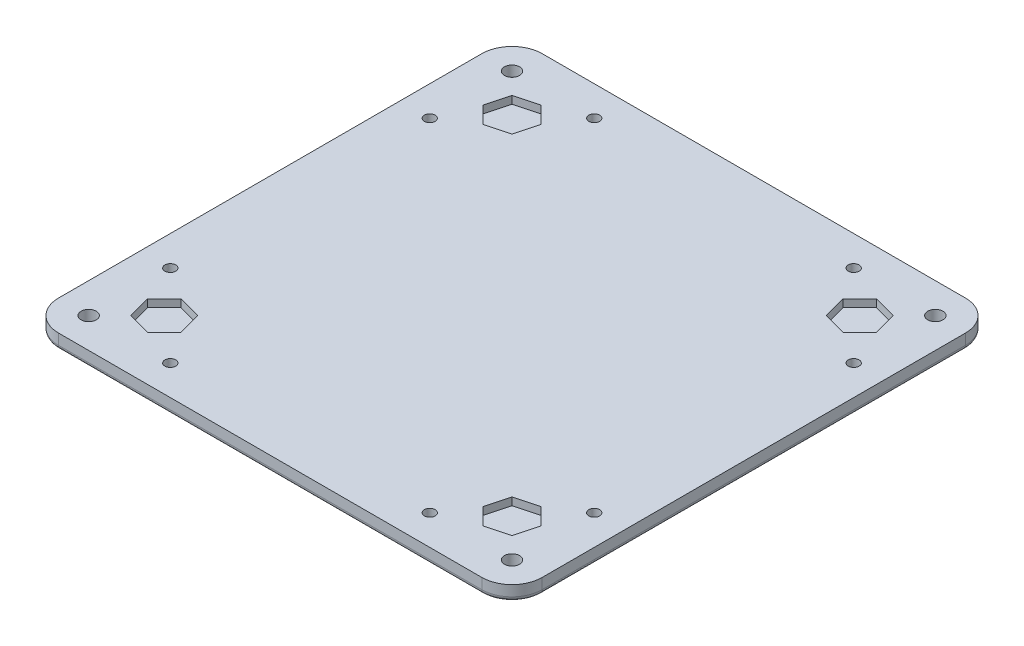
SolidWorks part; units mm, degrees
ref_plane "Front Plane" through (0, 0, 0) normal (0, 0, 1) x (1, 0, 0)
ref_plane "Top Plane" through (0, 0, 0) normal (0, 1, 0) x (1, 0, 0)
ref_plane "Right Plane" through (0, 0, 0) normal (1, 0, 0) x (0, 0, -1)
sketch "Sketch1" plane through (0, 0, 0) normal (0, 1, 0) x (1, 0, 0)
  line L1 (0, 0) -> (203.2, 0)
  line L2 (0, 0) -> (0, 203.2)
  line L3 (0, 203.2) -> (203.2, 203.2)
  line L4 (203.2, 0) -> (203.2, 203.2)
  dimension "D1" = 203.2
  dimension "D2" = 203.2
extrude "Boss-Extrude1" add sketch "Sketch1" along normal blind 6.35
fillet "Fillet1" radius 12.7 4 edges at (0, 3.175, -203.2) (0, 3.175, 0) (203.2, 3.175, 0) (203.2, 3.175, -203.2)
sketch "Sketch2" plane through (0, 0, 0) normal (0, -1, 0) x (1, 0, 0)
  circle A0 centre (12.7, -12.7) radius 3.175
  circle A1 centre (190.5, -12.7) radius 3.175
  circle A2 centre (190.5, -190.5) radius 3.175
  circle A3 centre (12.7, -190.5) radius 3.175
  arc A4 (190.5, -203.2) -> (203.2, -190.5) centre (190.5, -190.5) ccw construction
  arc A5 (12.7, 0) -> (0, -12.7) centre (12.7, -12.7) ccw construction
  dimension "D1" = 6.35
extrude "Cut-Extrude1" cut sketch "Sketch2" against normal through all
sketch "Sketch22" plane through (0, 6.35, 0) normal (0, 1, 0) x (1, 0, 0)
  line L17 (190.5, 203.2) -> (12.7, 203.2) construction
  line L18 (203.2, 12.7) -> (203.2, 190.5) construction
  line L21 (181.6542, 181.6542) -> (172.0521, 184.2271)
  line L22 (172.0521, 184.2271) -> (165.0229, 177.1979)
  line L23 (165.0229, 177.1979) -> (167.5958, 167.5958)
  line L24 (167.5958, 167.5958) -> (177.1979, 165.0229)
  line L25 (177.1979, 165.0229) -> (184.2271, 172.0521)
  line L26 (184.2271, 172.0521) -> (181.6542, 181.6542)
  line L27 (174.625, 174.625) -> (190.5, 190.5) construction
  line L28 (101.6, 203.2) -> (101.6, 0) construction
  line L29 (12.7, 0) -> (190.5, 0) construction
  line L30 (203.2, 101.6) -> (0, 101.6) construction
  line L31 (0, 190.5) -> (0, 12.7) construction
  line L32 (28.575, 174.625) -> (12.7, 190.5) construction
  line L33 (18.9729, 172.0521) -> (21.5458, 181.6542)
  line L34 (26.0021, 165.0229) -> (18.9729, 172.0521)
  line L35 (35.6042, 167.5958) -> (26.0021, 165.0229)
  line L36 (38.1771, 177.1979) -> (35.6042, 167.5958)
  line L37 (31.1479, 184.2271) -> (38.1771, 177.1979)
  line L38 (21.5458, 181.6542) -> (31.1479, 184.2271)
  line L39 (174.625, 28.575) -> (190.5, 12.7) construction
  line L40 (184.2271, 31.1479) -> (181.6542, 21.5458)
  line L41 (177.1979, 38.1771) -> (184.2271, 31.1479)
  line L42 (167.5958, 35.6042) -> (177.1979, 38.1771)
  line L43 (165.0229, 26.0021) -> (167.5958, 35.6042)
  line L44 (172.0521, 18.9729) -> (165.0229, 26.0021)
  line L45 (181.6542, 21.5458) -> (172.0521, 18.9729)
  line L46 (28.575, 28.575) -> (12.7, 12.7) construction
  line L47 (21.5458, 21.5458) -> (31.1479, 18.9729)
  line L48 (31.1479, 18.9729) -> (38.1771, 26.0021)
  line L49 (38.1771, 26.0021) -> (35.6042, 35.6042)
  line L50 (35.6042, 35.6042) -> (26.0021, 38.1771)
  line L51 (26.0021, 38.1771) -> (18.9729, 31.1479)
  line L52 (18.9729, 31.1479) -> (21.5458, 21.5458)
  circle A0 centre (174.625, 174.625) radius 8.609 construction
  circle A1 centre (28.575, 174.625) radius 8.609 construction
  circle A2 centre (174.625, 28.575) radius 8.609 construction
  circle A3 centre (28.575, 28.575) radius 8.609 construction
  dimension "D5" = 17.218
  dimension "D3" = 28.575
  dimension "D4" = 28.575
extrude "Cut-Extrude2" cut sketch "Sketch22" against normal blind 3.175
fillet "Fillet2" radius 1.905 12 edges at (3.7197, 0, -3.7197) (101.6, 0, 0) (199.4803, 0, -3.7197) (203.2, 0, -101.6) (199.4803, 0, -199.4803) (101.6, 0, -203.2) (3.7197, 0, -199.4803) (0, 0, -101.6) (12.7, 0, -15.875) (190.5, 0, -15.875) (190.5, 0, -193.675) (12.7, 0, -193.675)
sketch "Sketch28" plane through (0, 6.35, 0) normal (0, 1, 0) x (1, 0, 0)
  line L0 (190.5, 203.2) -> (12.7, 203.2) construction
  line L1 (203.2, 12.7) -> (203.2, 190.5) construction
  line L2 (12.7, 0) -> (190.5, 0) construction
  line L4 (0, 190.5) -> (0, 12.7) construction
  circle A0 centre (47.117, 190.627) radius 2.286
  circle A1 centre (156.083, 190.627) radius 2.286
  circle A2 centre (190.627, 156.083) radius 2.286
  circle A3 centre (190.627, 47.117) radius 2.286
  circle A4 centre (156.083, 12.573) radius 2.286
  circle A5 centre (47.117, 12.573) radius 2.286
  circle A6 centre (12.573, 156.083) radius 2.286
  circle A7 centre (12.573, 47.117) radius 2.286
  dimension "D4" = 4.572
  dimension "D1" = 12.573
  dimension "D2" = 12.573
  dimension "D3" = 12.573
  dimension "D5" = 12.573
  dimension "D6" = 47.117
  dimension "D7" = 47.117
  dimension "D8" = 47.117
  dimension "D9" = 47.117
extrude "Cut-Extrude3" cut sketch "Sketch28" against normal through all
